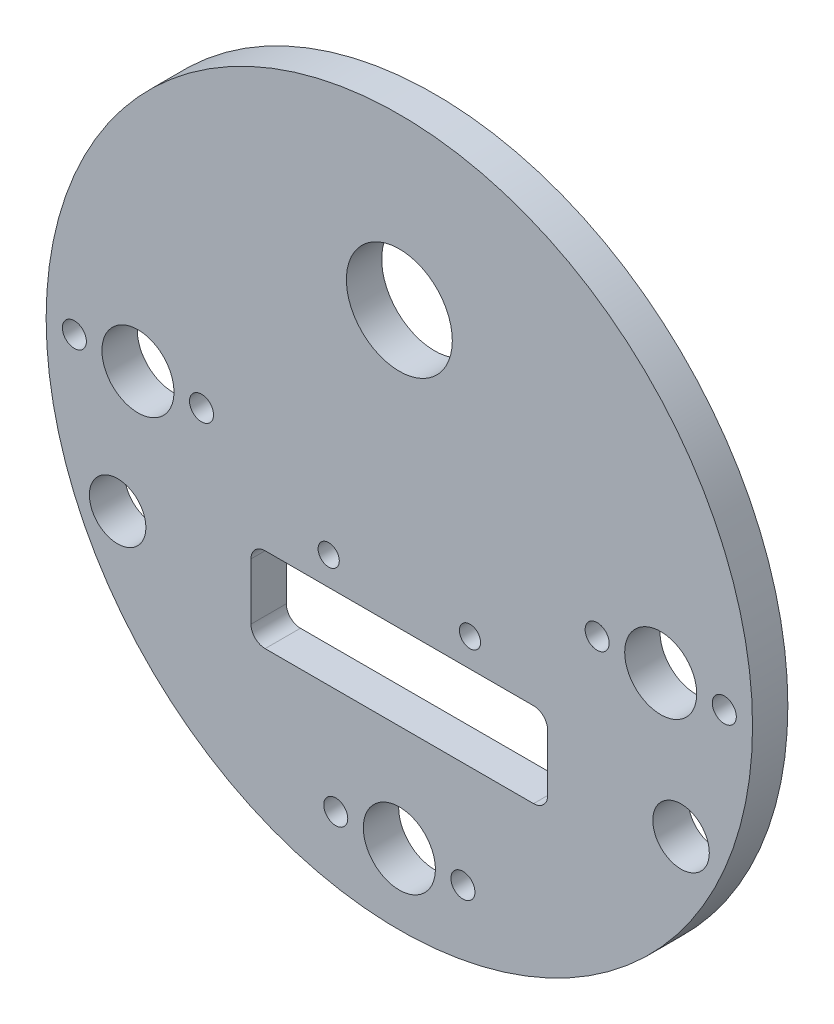
SolidWorks part; units mm, degrees
material "Acrylic (Medium-high impact)"
ref_plane "Front Plane" through (0, 0, 0) normal (0, 0, 1) x (1, 0, 0)
ref_plane "Top Plane" through (0, 0, 0) normal (0, 1, 0) x (1, 0, 0)
ref_plane "Right Plane" through (0, 0, 0) normal (1, 0, 0) x (0, 0, -1)
sketch "Sketch1" plane through (0, 0, 0) normal (0, 0, 1) x (1, 0, 0)
  circle A0 centre (0, 0) radius 50
  dimension "D1" = 100
extrude "Boss-Extrude1" add sketch "Sketch1" along normal blind 5
hole_wizard "Ø10.2 (10.2) Diameter Hole1" positions "Sketch5" profile "Sketch6" hole size "Ø10.2" standard "ISO"
sketch "Sketch5" plane through (0, 0, 0) normal (0, 0, -1) x (-1, 0, 0)
  point P4 (37, 0)
  point P17 (-37, 0)
  point P21 (0, -37) [skipped]
  point P23 (0, -40)
  dimension "D1" = 3
  dimension "D3" = 37
sketch "Sketch6" plane through (-37, 0, 0) normal (1, 0, 0) x (0, 1, 0)
  line L0 (0, 0) -> (0, 5)
  line L1 (0, 5) -> (5.1, 5)
  line L2 (5.1, 5) -> (5.1, 0)
  line L5 (5.1, 0) -> (0, 0)
  line L11 (0, -6.35) -> (0, 107.95) construction
  dimension "Thru Hole Dia." = 10.2
  dimension "Thru Hole Depth" = 5
hole_wizard "M3 Clearance Hole1" positions "Sketch7" profile "Sketch8" hole size "M3" standard "ISO" end condition through all
sketch "Sketch7" plane through (0, 0, 5) normal (0, 0, 1) x (1, 0, 0)
  circle A0 centre (37, 0) radius 5.1 construction
  circle A1 centre (0, -40) radius 5.1 construction
  point P0 (46, 0)
  point P2 (28, 0)
  point P11 (9, -40)
  point P13 (-9, -40)
  point P46 (-46, 0)
  point P47 (-28, 0)
  dimension "D2" = 9
  dimension "D1" = 9
  dimension "D4" = 9
  dimension "D5" = 9
  dimension "D6" = 2
  dimension "D3" = 40
sketch "Sketch8" plane through (46, 0, 5) normal (1, 0, 0) x (0, -1, 0)
  line L0 (0, 0) -> (0, 5)
  line L1 (0, 5) -> (1.7, 5)
  line L2 (1.7, 5) -> (1.7, 0)
  line L5 (1.7, 0) -> (0, 0)
  line L11 (0, -6.35) -> (0, 107.95) construction
  dimension "Thru Hole Dia." = 3.4
  dimension "Thru Hole Depth" = 5
sketch "Sketch9" plane through (0, 0, 5) normal (0, 0, 1) x (1, 0, 0)
  circle A0 centre (0, 26) radius 7.5
  dimension "D1" = 15
  dimension "D2" = 26
extrude "Cut-Extrude1" cut sketch "Sketch9" against normal blind 10 contours A0
sketch "Sketch10" plane through (0, 0, 5) normal (0, 0, 1) x (1, 0, 0)
  line L1 (-19, -13) -> (19, -13)
  line L2 (-21, -15) -> (-21, -23)
  line L3 (-19, -25) -> (19, -25)
  line L4 (21, -15) -> (21, -23)
  circle A0 centre (0, 0) radius 50 construction
  arc A1 (-19, -13) -> (-21, -15) centre (-19, -15) ccw
  circle A2 centre (10, -9) radius 1.5
  circle A3 centre (-10, -9) radius 1.5
  arc A4 (-21, -23) -> (-19, -25) centre (-19, -23) ccw
  arc A5 (19, -25) -> (21, -23) centre (19, -23) ccw
  arc A6 (21, -15) -> (19, -13) centre (19, -15) ccw
  point P8 (-21, -13)
  point P16 (-21, -25)
  point P19 (21, -25)
  dimension "D5" = 3
  dimension "D6" = 3
  dimension "D7" = 16
  dimension "D9" = 20
  dimension "D11" = 2
  dimension "D1" = 12
  dimension "D2" = 42
  dimension "D3" = 25
  dimension "D4" = 21
  dimension "D8" = 16
  dimension "D10" = 11
extrude "Cut-Extrude2" cut sketch "Sketch10" against normal blind 10
sketch "Sketch11" plane through (0, 0, 5) normal (0, 0, 1) x (1, 0, 0)
  line L0 (0, 0) -> (-39.8775, -18.5952) construction
  line L1 (0, 0) -> (0, -29.0371) construction
  circle A0 centre (-39.8775, -18.5952) radius 4
  circle A1 centre (39.8775, -18.5952) radius 4
  dimension "D1" = 8
  dimension "D2" = 65
  dimension "D3" = 44
extrude "Cut-Extrude3" cut sketch "Sketch11" against normal blind 10
